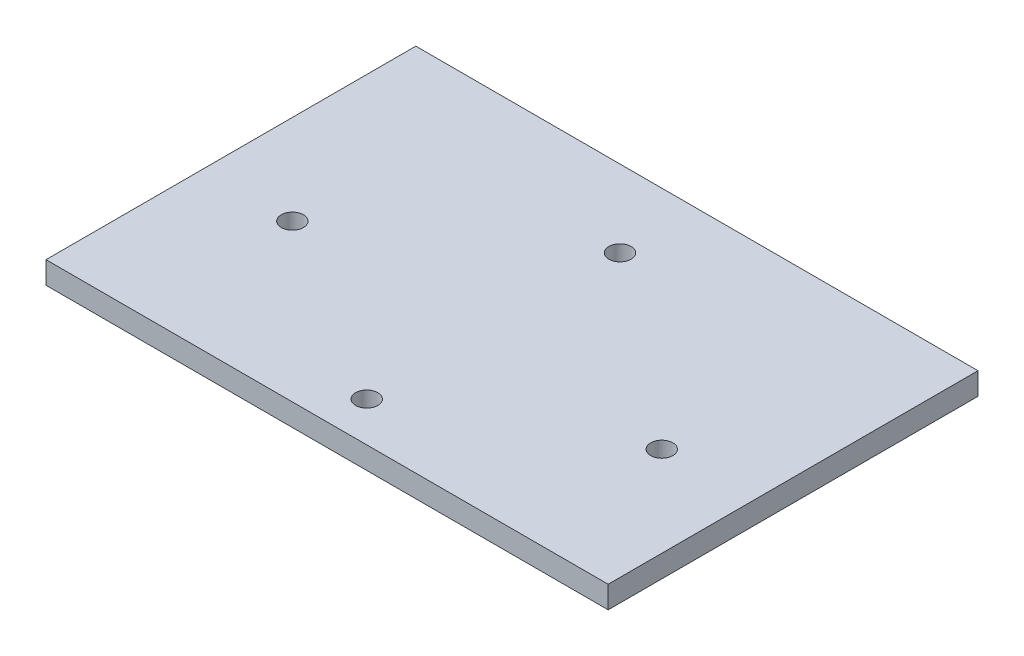
SolidWorks part; units mm, degrees
material "ABS PC"
ref_plane "Front Plane" through (0, 0, 0) normal (0, 0, 1) x (1, 0, 0)
ref_plane "Top Plane" through (0, 0, 0) normal (0, 1, 0) x (1, 0, 0)
ref_plane "Right Plane" through (0, 0, 0) normal (1, 0, 0) x (0, 0, -1)
sketch "Sketch2" plane through (0, 0, 0) normal (0, 1, 0) x (1, 0, 0)
  line L1 (-38, 25) -> (38, 25)
  line L2 (-38, 25) -> (-38, -25)
  line L3 (-38, -25) -> (38, -25)
  line L4 (38, 25) -> (38, -25)
  line L5 (-38, 25) -> (38, -25) construction
  line L6 (-38, -25) -> (38, 25) construction
  circle A0 centre (25.8167, -5.5665) radius 1.5
  circle A1 centre (0, 14.599) radius 1.5
  circle A2 centre (-25.8575, -3.8343) radius 1.5
  circle A3 centre (0, -19.6404) radius 1.5
  point P0 (0, 0)
  dimension "D3" = 3
  dimension "D4" = 3
  dimension "D5" = 3
  dimension "D6" = 3
  dimension "D1" = 76
  dimension "D2" = 50
extrude "Boss-Extrude1" add sketch "Sketch2" along normal blind 3
